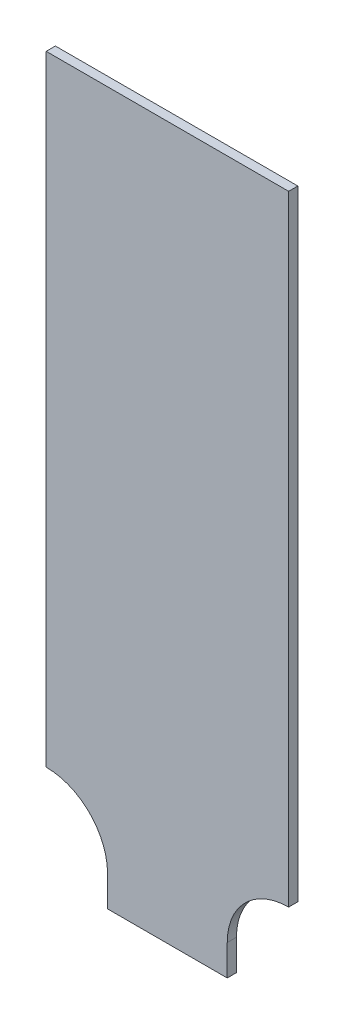
SolidWorks part; units mm, degrees
ref_plane "Face" through (0, 0, 0) normal (0, 0, 1) x (1, 0, 0)
ref_plane "Dessus" through (0, 0, 0) normal (0, 1, 0) x (1, 0, 0)
ref_plane "Droite" through (0, 0, 0) normal (1, 0, 0) x (0, 0, -1)
sketch "Esquisse1" plane through (0, 0, 0) normal (0, 0, 1) x (1, 0, 0)
  line L0 (0, 0) -> (0, 232) construction
  line L1 (39.5, 232) -> (-39.5, 232)
  line L2 (-39.5, 232) -> (-39.5, 30)
  line L3 (19.5, 0) -> (-19.5, 0)
  line L4 (-19.5, 0) -> (-19.5, 10)
  line L5 (-39.5, 30) -> (-39.5, 0) construction
  line L6 (39.5, 30) -> (39.5, 0) construction
  line L7 (19.5, 0) -> (19.5, 10)
  line L8 (39.5, 232) -> (39.5, 30)
  arc A0 (-39.5, 30) -> (-19.5, 10) centre (-39.5, 10) cw
  arc A1 (39.5, 30) -> (19.5, 10) centre (39.5, 10) ccw
  dimension "D3" = 20
  dimension "D1" = 232
  dimension "D2" = 39.5
  dimension "D4" = 30
extrude "Extrusion1" add sketch "Esquisse1" along normal blind 3
